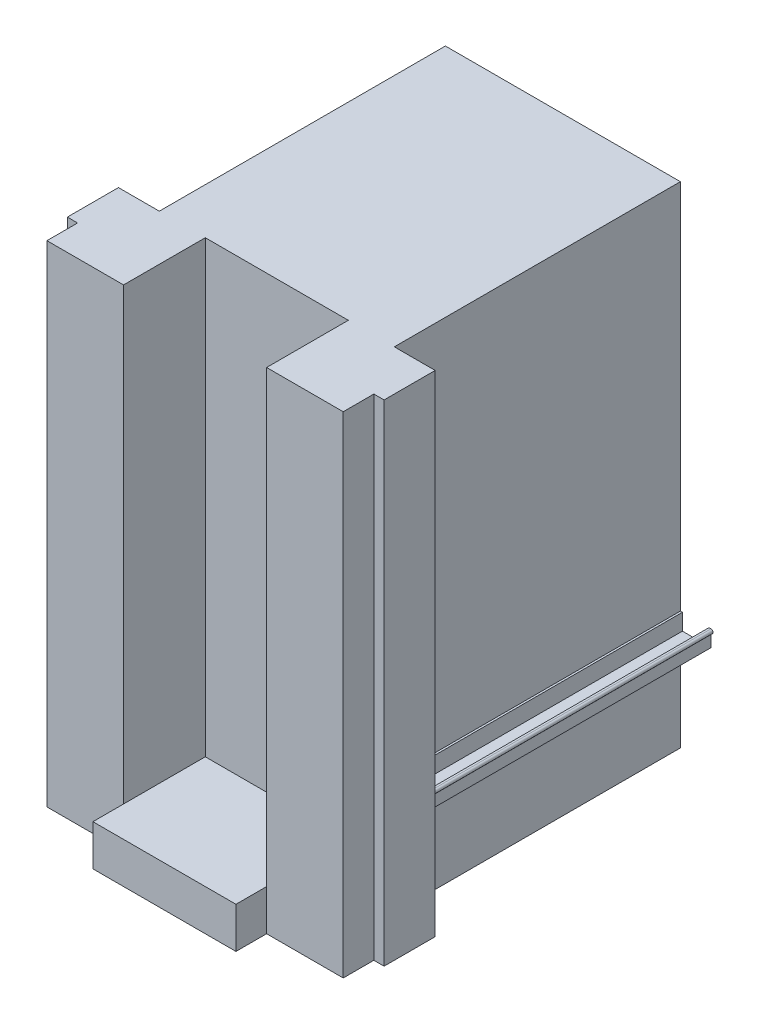
SolidWorks part; units mm, degrees
ref_plane "前基準面" through (0, 0, 0) normal (0, 0, 1) x (1, 0, 0)
ref_plane "上基準面" through (0, 0, 0) normal (0, 1, 0) x (1, 0, 0)
ref_plane "右基準面" through (0, 0, 0) normal (1, 0, 0) x (0, 0, -1)
sketch "草圖1" plane through (0, 0, 0) normal (0, 0, 1) x (1, 0, 0)
  line L0 (-725, 309.4582) -> (-725, 249.4582)
  line L1 (608.7081, 249.409) -> (608.7081, 239.4582) construction
  line L2 (584.9508, 329.4582) -> (575, 329.4582)
  line L3 (725, 329.4582) -> (715.0492, 329.4582)
  line L4 (715.0492, 249.409) -> (584.9508, 249.409)
  line L5 (584.9508, 329.4582) -> (584.9508, 249.409)
  line L6 (715.0492, 329.4582) -> (715.0492, 249.409)
  line L7 (-725, 249.4582) -> (-692.0261, 239.4582)
  line L8 (-692.0261, 239.4582) -> (-575, 239.4582)
  line L9 (-575, 239.4582) -> (-575, -250.5418)
  line L10 (-608.7081, 249.409) -> (-608.7081, 239.4582) construction
  line L11 (-715.0492, 329.4582) -> (-715.0492, 249.409)
  line L12 (-584.9508, 329.4582) -> (-584.9508, 249.409)
  line L13 (-715.0492, 249.409) -> (-584.9508, 249.409)
  line L14 (-725, 329.4582) -> (-715.0492, 329.4582)
  line L15 (-584.9508, 329.4582) -> (-575, 329.4582)
  line L16 (0, 2585.9131) -> (0, -269.0275)
  line L18 (692.0261, 239.4582) -> (575, 239.4582)
  line L19 (725, 249.4582) -> (692.0261, 239.4582)
  line L20 (725, 309.4582) -> (725, 249.4582)
  line L21 (575, 239.4582) -> (575, -250.5418)
  line L22 (-575, 2149.4582) -> (575, 2149.4582)
  line L23 (-575, 2149.4582) -> (-575, 329.4582)
  line L24 (-575, -250.5418) -> (575, -250.5418)
  line L25 (575, 2149.4582) -> (575, 329.4582)
  line L26 (-575, 2149.4582) -> (575, -250.5418) construction
  line L27 (-575, -250.5418) -> (575, 2149.4582) construction
  arc A0 (-725, 329.4582) -> (-725, 309.4582) centre (-725, 319.4582) ccw
  arc A1 (725, 329.4582) -> (725, 309.4582) centre (725, 319.4582) cw
  point P29 (0, 949.4582)
  point P34 (0, 375.7368)
  point P35 (0, 2585.9131)
  dimension "D2" = 10
  dimension "D1" = 90
  dimension "D3" = 60
  dimension "D4" = 490
  dimension "D5" = 2400
  dimension "D6" = 1150
extrude "填料-伸長1" add sketch "草圖1" along normal blind 1400 contours L14 A0 L0 L7 L8 L9 L24 L16 L22 L23 L15 L12 L13 L11 | A1 L3 L6 L4 L5 L2 L25 L22 L16 L24 L21 L18 L19 L20
sketch "草圖3" plane through (0, 0, 1400) normal (0, 0, 1) x (1, 0, 0)
  line L0 (0, -250.5418) -> (0, 2149.4582) construction
  line L1 (775, 2149.4582) -> (-775, 2149.4582)
  line L2 (-775, 2149.4582) -> (-775, -250.5418)
  line L3 (-775, -250.5418) -> (775, -250.5418)
  line L5 (775, 2149.4582) -> (775, -250.5418)
  line L8 (-575, 2149.4582) -> (575, 2149.4582) construction
  line L9 (-575, -250.5418) -> (575, -250.5418) construction
  line L10 (-725, 309.4582) -> (-725, 249.4582) construction
  point P5 (0, -364.9865)
  point P14 (-725, 279.4582)
  dimension "D1" = 50
extrude "填料-伸長2" add sketch "草圖3" along normal blind 400
sketch "草圖4" plane through (0, 2149.4582, 0) normal (0, 1, 0) x (1, 0, 0)
  line L0 (0, -551.9756) -> (0, -2248.0244) construction
  line L1 (-775, -1800) -> (-725, -1800)
  line L2 (-775, -1800) -> (-775, -1650)
  line L3 (-775, -1650) -> (-725, -1650)
  line L4 (-725, -1800) -> (-725, -1650)
  line L5 (725, -1800) -> (725, -1650)
  line L6 (775, -1650) -> (725, -1650)
  line L7 (775, -1800) -> (775, -1650)
  line L8 (775, -1800) -> (725, -1800)
  line L9 (775, -1800) -> (-775, -1800) construction
  line L10 (-350, -1800) -> (350, -1800)
  line L11 (-350, -1800) -> (-350, -1400)
  line L12 (-350, -1400) -> (350, -1400)
  line L13 (350, -1800) -> (350, -1400)
  line L14 (-575, -1400) -> (-775, -1400) construction
  point P18 (0, -1400)
  dimension "D1" = 50
  dimension "D2" = 150
  dimension "D3" = 700
extrude "除料-伸長1" cut sketch "草圖4" against normal through all
sketch "草圖5" plane through (0, 0, 1800) normal (0, 0, 1) x (1, 0, 0)
  line L0 (350, -250.5418) -> (350, 2149.4582) construction
  line L1 (-350, -250.5418) -> (350, -250.5418)
  line L2 (-350, -250.5418) -> (-350, -50.5418)
  line L3 (-350, -50.5418) -> (350, -50.5418)
  line L4 (350, -250.5418) -> (350, -50.5418)
  dimension "D1" = 200
extrude "填料-伸長3" add sketch "草圖5" along normal blind 150 and the other way up to surface (1800 mm away)
